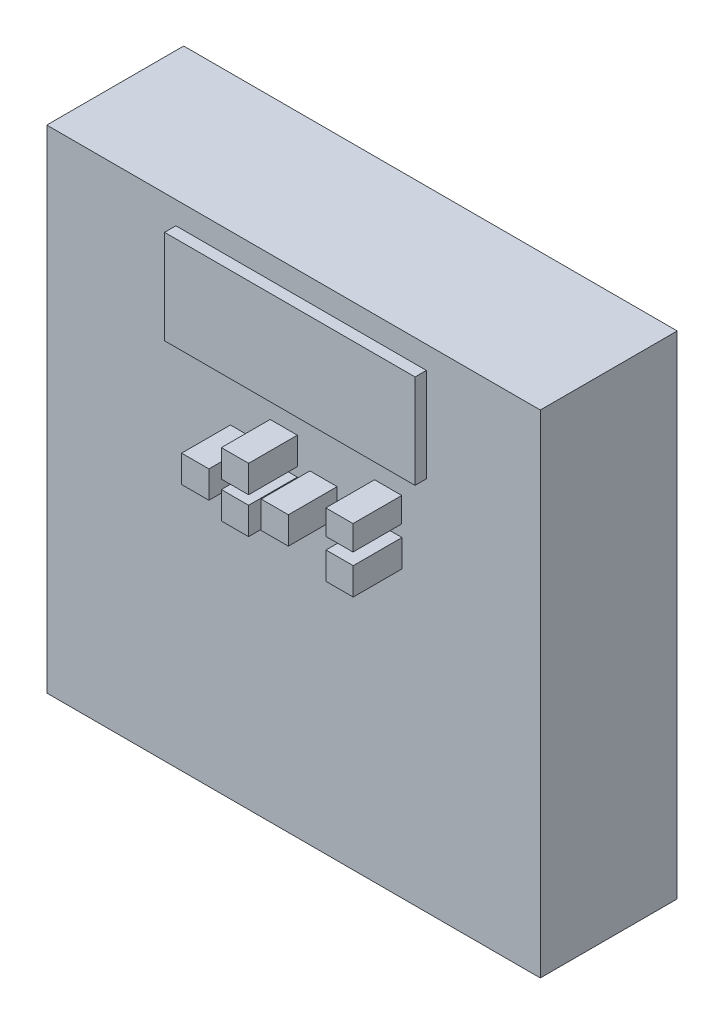
SolidWorks part; units mm, degrees
ref_plane "Front Plane" through (0, 0, 0) normal (0, 0, 1) x (1, 0, 0)
ref_plane "Top Plane" through (0, 0, 0) normal (0, 1, 0) x (1, 0, 0)
ref_plane "Right Plane" through (0, 0, 0) normal (1, 0, 0) x (0, 0, -1)
sketch "Sketch1" plane through (0, 0, 0) normal (0, 0, 1) x (1, 0, 0)
  line L1 (55.2958, -55.1117) -> (-55.2958, -55.1117)
  line L2 (55.2958, -55.1117) -> (55.2958, 55.1116)
  line L3 (55.2958, 55.1116) -> (-55.2958, 55.1116)
  line L4 (-55.2958, -55.1117) -> (-55.2958, 55.1116)
  line L5 (55.2958, -55.1117) -> (-55.2958, 55.1116) construction
  line L6 (55.2958, 55.1116) -> (-55.2958, -55.1117) construction
  point P0 (0, 0)
extrude "Boss-Extrude1" add sketch "Sketch1" along normal blind 30.6832
sketch "Sketch3" plane through (0, 0, 30.6832) normal (0, 0, 1) x (1, 0, 0)
  line L0 (-55.2958, 55.1116) -> (-55.2958, -55.1117) construction
  line L1 (-26.3652, 50.0316) -> (29.7688, 50.0316)
  line L2 (-26.3652, 50.0316) -> (-26.3652, 28.9877)
  line L3 (-26.3652, 28.9877) -> (29.7688, 28.9877)
  line L4 (29.7688, 50.0316) -> (29.7688, 28.9877)
  line L5 (55.2958, 55.1116) -> (-55.2958, 55.1116) construction
  dimension "D1" = 28.9306
  dimension "D2" = 5.08
extrude "Boss-Extrude2" add sketch "Sketch3" along normal blind 2.54
sketch "Sketch6" plane through (0, 0, 30.6832) normal (0, 0, 1) x (1, 0, 0)
  line L0 (-26.3652, 28.9877) -> (29.7688, 28.9877) construction
  line L1 (0.8509, 16.8973) -> (-5.2451, 16.8973)
  line L2 (0.8509, 16.8973) -> (0.8509, 23.006)
  line L3 (0.8509, 23.006) -> (-5.2451, 23.0061)
  line L4 (-5.2451, 16.8973) -> (-5.2451, 23.0061)
  line L5 (-55.2958, 55.1116) -> (-55.2958, -55.1117) construction
  line L6 (-26.3652, 28.9877) -> (29.7688, 28.9877) construction
  line L7 (-14.1478, 17.4815) -> (-8.0391, 17.4815)
  line L8 (-14.1478, 17.4815) -> (-14.1478, 11.3855)
  line L9 (-14.1478, 11.3855) -> (-8.0391, 11.3855)
  line L10 (-8.0391, 17.4815) -> (-8.0391, 11.3855)
  line L12 (3.6703, 17.4815) -> (9.7688, 17.4815)
  line L13 (3.6703, 17.4815) -> (3.6703, 11.3855)
  line L14 (3.6703, 11.3855) -> (9.7688, 11.3855)
  line L15 (9.7688, 17.4815) -> (9.7688, 11.3855)
  line L16 (-5.2451, 14.8653) -> (0.8509, 14.8653)
  line L17 (-5.2451, 14.8653) -> (-5.2451, 8.7693)
  line L18 (-5.2451, 8.7693) -> (0.8509, 8.7693)
  line L19 (0.8509, 14.8653) -> (0.8509, 8.7693)
  line L20 (18.1508, 23.006) -> (24.2468, 23.006)
  line L21 (18.1508, 23.006) -> (18.1508, 17.4815)
  line L22 (18.1508, 17.4815) -> (24.2468, 17.4815)
  line L23 (24.2468, 23.006) -> (24.2468, 17.4815)
  line L24 (18.1991, 14.8653) -> (24.2951, 14.8653)
  line L25 (18.1991, 14.8653) -> (18.1991, 8.7693)
  line L26 (18.1991, 8.7693) -> (24.2951, 8.7693)
  line L27 (24.2951, 14.8653) -> (24.2951, 8.7693)
  dimension "D1" = 5.9817
  dimension "D2" = 50.0507
  dimension "D3" = 6.1087
  dimension "D4" = 6.096
  dimension "D5" = 11.5062
  dimension "D6" = 6.1087
  dimension "D7" = 6.096
  dimension "D8" = 2.794
  dimension "D9" = 6.0985
  dimension "D10" = 6.096
  dimension "D11" = 11.7094
  dimension "D12" = 11.5062
  dimension "D13" = 2.794
  dimension "D14" = 2.8194
  dimension "D15" = 2.032
  dimension "D16" = 6.096
  dimension "D17" = 17.3482
  dimension "D18" = 6.096
  dimension "D19" = 6.096
  dimension "D20" = 6.096
  dimension "D21" = 2.6162
  dimension "D22" = 8.382
  dimension "D23" = 20.2184
extrude "Boss-Extrude3" add sketch "Sketch6" along normal blind 10.922
